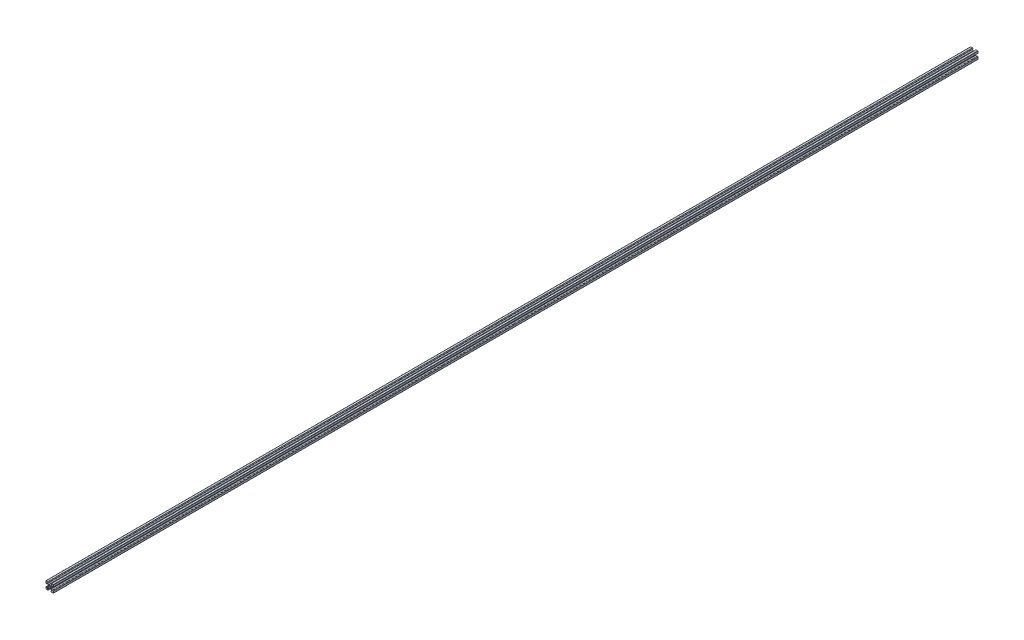
SolidWorks part; units mm, degrees
material "6061-T6 (SS)"
ref_plane "Front Plane" through (0, 0, 0) normal (0, 0, 1) x (1, 0, 0)
ref_plane "Top Plane" through (0, 0, 0) normal (0, 1, 0) x (1, 0, 0)
ref_plane "Right Plane" through (0, 0, 0) normal (1, 0, 0) x (0, 0, -1)
sketch "Sketch1" plane through (0, 0, 0) normal (0, 0, 1) x (1, 0, 0)
  line L1 (9.5, -10) -> (-9.5, -10)
  line L2 (10, -9.5) -> (10, 9.5)
  line L3 (9.5, 10) -> (-9.5, 10)
  line L4 (-10, -9.5) -> (-10, 9.5)
  line L5 (10, -10) -> (-10, 10) construction
  line L6 (10, 10) -> (-10, -10) construction
  circle A0 centre (0, 0) radius 2.1
  arc A1 (-9.5, 10) -> (-10, 9.5) centre (-9.5, 9.5) ccw
  arc A2 (10, 9.5) -> (9.5, 10) centre (9.5, 9.5) ccw
  arc A3 (9.5, -10) -> (10, -9.5) centre (9.5, -9.5) ccw
  arc A4 (-9.5, -10) -> (-10, -9.5) centre (-9.5, -9.5) cw
  point P0 (0, 0)
  line B0 (0, 0) -> (0, 10) construction
  line B1 (0, 3.69) -> (-0.21, 3.9)
  line B2 (-0.21, 3.9) -> (-2.8393, 3.9)
  line B3 (-2.8393, 3.9) -> (-5.5, 6.5607)
  line B4 (-5.5, 6.5607) -> (-5.5, 8.2)
  line B5 (-5.5, 8.2) -> (-3.125, 8.2)
  line B6 (-3.125, 8.2) -> (-3.125, 8.545)
  line B7 (-3.125, 8.545) -> (-4.58, 10)
  line B8 (-4.58, 10) -> (4.58, 10)
  line B9 (0, 0) -> (-5.9132, 5.9132) construction
  line B10 (3.125, 8.545) -> (4.58, 10)
  line B11 (3.125, 8.2) -> (3.125, 8.545)
  line B12 (5.5, 8.2) -> (3.125, 8.2)
  line B13 (5.5, 6.5607) -> (5.5, 8.2)
  line B14 (2.8393, 3.9) -> (5.5, 6.5607)
  line B15 (0.21, 3.9) -> (2.8393, 3.9)
  line B16 (0, 3.69) -> (0.21, 3.9)
  line B17 (0, 0) -> (-10, 0) construction
  line B18 (-3.69, 0) -> (-3.9, -0.21)
  line B19 (-3.9, -0.21) -> (-3.9, -2.8393)
  line B20 (-3.9, -2.8393) -> (-6.5607, -5.5)
  line B21 (-6.5607, -5.5) -> (-8.2, -5.5)
  line B22 (-8.2, -5.5) -> (-8.2, -3.125)
  line B23 (-8.2, -3.125) -> (-8.545, -3.125)
  line B24 (-8.545, -3.125) -> (-10, -4.58)
  line B25 (-10, -4.58) -> (-10, 4.58)
  line B26 (0, 0) -> (-5.9132, -5.9132) construction
  line B27 (-8.545, 3.125) -> (-10, 4.58)
  line B28 (-8.2, 3.125) -> (-8.545, 3.125)
  line B29 (-8.2, 5.5) -> (-8.2, 3.125)
  line B30 (-6.5607, 5.5) -> (-8.2, 5.5)
  line B31 (-3.9, 2.8393) -> (-6.5607, 5.5)
  line B32 (-3.9, 0.21) -> (-3.9, 2.8393)
  line B33 (-3.69, 0) -> (-3.9, 0.21)
  line B34 (0, 0) -> (0, -10) construction
  line B35 (0, -3.69) -> (0.21, -3.9)
  line B36 (0.21, -3.9) -> (2.8393, -3.9)
  line B37 (2.8393, -3.9) -> (5.5, -6.5607)
  line B38 (5.5, -6.5607) -> (5.5, -8.2)
  line B39 (5.5, -8.2) -> (3.125, -8.2)
  line B40 (3.125, -8.2) -> (3.125, -8.545)
  line B41 (3.125, -8.545) -> (4.58, -10)
  line B42 (4.58, -10) -> (-4.58, -10)
  line B43 (0, 0) -> (5.9132, -5.9132) construction
  line B44 (-3.125, -8.545) -> (-4.58, -10)
  line B45 (-3.125, -8.2) -> (-3.125, -8.545)
  line B46 (-5.5, -8.2) -> (-3.125, -8.2)
  line B47 (-5.5, -6.5607) -> (-5.5, -8.2)
  line B48 (-2.8393, -3.9) -> (-5.5, -6.5607)
  line B49 (-0.21, -3.9) -> (-2.8393, -3.9)
  line B50 (0, -3.69) -> (-0.21, -3.9)
  line B51 (0, 0) -> (10, 0) construction
  line B52 (3.69, 0) -> (3.9, 0.21)
  line B53 (3.9, 0.21) -> (3.9, 2.8393)
  line B54 (3.9, 2.8393) -> (6.5607, 5.5)
  line B55 (6.5607, 5.5) -> (8.2, 5.5)
  line B56 (8.2, 5.5) -> (8.2, 3.125)
  line B57 (8.2, 3.125) -> (8.545, 3.125)
  line B58 (8.545, 3.125) -> (10, 4.58)
  line B59 (10, 4.58) -> (10, -4.58)
  line B60 (0, 0) -> (5.9132, 5.9132) construction
  line B61 (8.545, -3.125) -> (10, -4.58)
  line B62 (8.2, -3.125) -> (8.545, -3.125)
  line B63 (8.2, -5.5) -> (8.2, -3.125)
  line B64 (6.5607, -5.5) -> (8.2, -5.5)
  line B65 (3.9, -2.8393) -> (6.5607, -5.5)
  line B66 (3.9, -0.21) -> (3.9, -2.8393)
  line B67 (3.69, 0) -> (3.9, -0.21)
  dimension "D1" = 4.2
  dimension "D3" = 0.5
  dimension "D2" = 20
sketch_block_instance "V Slot 1-4"
sketch_block "V Slot 1" parameters "D1"=10, "D2"=11, "D3"=4.3, "D4"=1.8, "D5"=0.21, "D6"=45, "D7"=9.16, "D8"=1.5, "D9"=6.25
sketch_block_instance "V Slot 1-5"
sketch_block_instance "V Slot 1-6"
sketch_block_instance "V Slot 1-7"
extrude "Boss-Extrude1" add sketch "Sketch1" along normal blind 2500 contours B67 B52 B53 B54 B55 B56 B57 B58 L2 A2 L3 B10 B11 B12 B13 B14 B15 B16 B1 B2 B3 B4 B5 B6 B7 A1 L4 B27 B28 B29 B30 B31 B32 B33 B18 B19 B20 B21 B22 B23 B24 A4 L1 B44 B45 B46 B47 B48 B49
